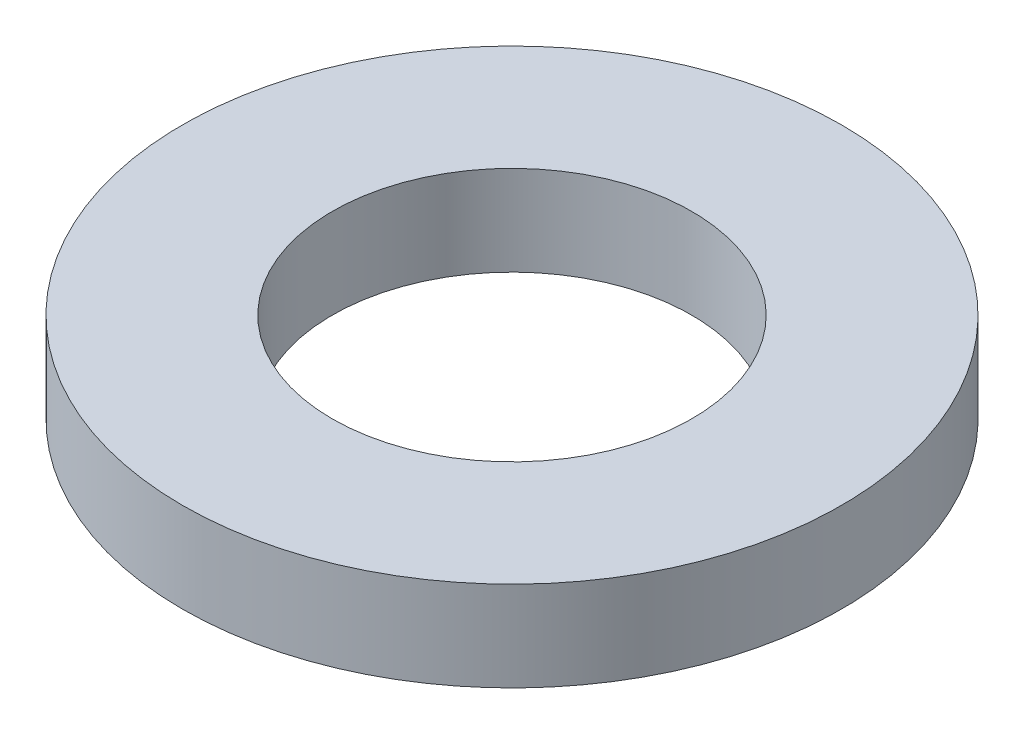
SolidWorks part; units mm, degrees
material "A-玻璃纤维"
ref_plane "前视基准面" through (0, 0, 0) normal (0, 0, 1) x (1, 0, 0)
ref_plane "上视基准面" through (0, 0, 0) normal (0, 1, 0) x (1, 0, 0)
ref_plane "右视基准面" through (0, 0, 0) normal (1, 0, 0) x (0, 0, -1)
sketch "草图1" plane through (0, 0, 0) normal (0, 1, 0) x (1, 0, 0)
  circle A0 centre (0, 0) radius 6
  circle A1 centre (0, 0) radius 11
  dimension "D1" = 12
  dimension "D2" = 22
extrude "凸台-拉伸1" add sketch "草图1" along normal blind 3
